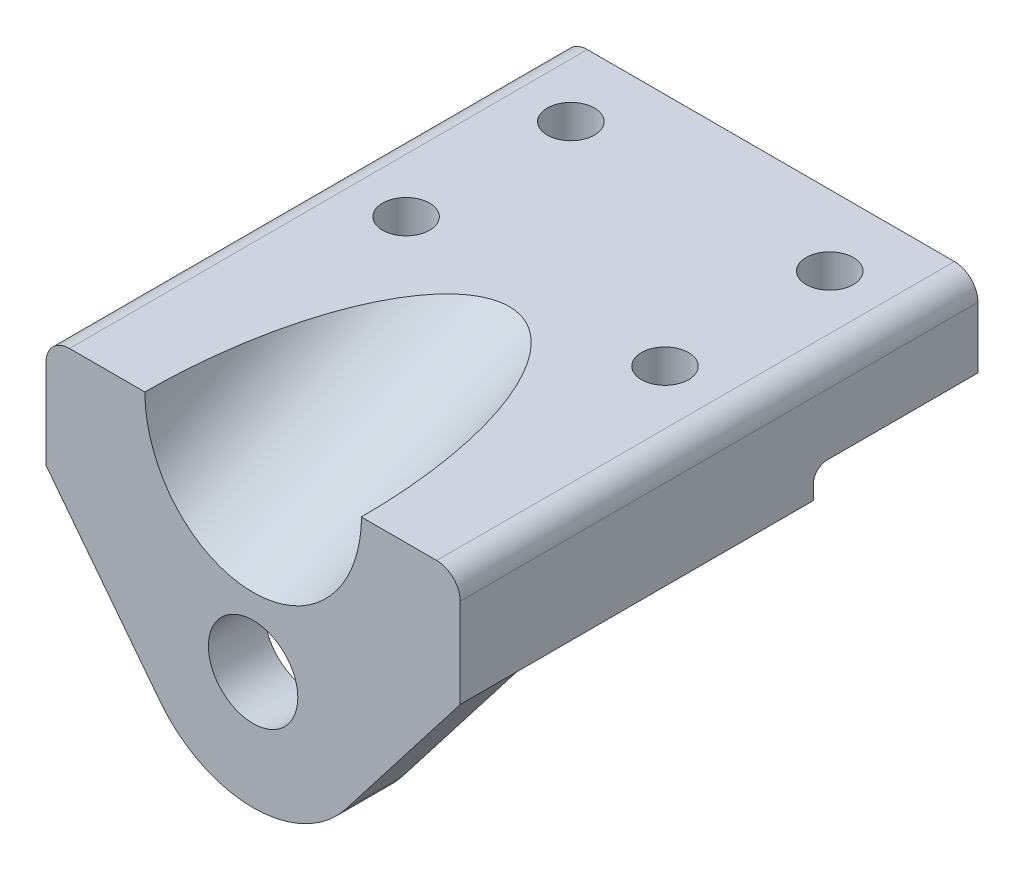
SolidWorks part; units mm, degrees
ref_plane "Front Plane" through (0, 0, 0) normal (0, 0, 1) x (1, 0, 0)
ref_plane "Top Plane" through (0, 0, 0) normal (0, 1, 0) x (1, 0, 0)
ref_plane "Right Plane" through (0, 0, 0) normal (1, 0, 0) x (0, 0, -1)
sketch "Sketch1" plane through (0, 0, 0) normal (0, 1, 0) x (1, 0, 0)
  line L0 (-44, 0) -> (44, 0)
  line L1 (44, 0) -> (44, 110)
  line L2 (44, 110) -> (-44, 110)
  line L3 (-44, 110) -> (-44, 0)
  circle A0 centre (-27.5, 95) radius 5
  circle A1 centre (-27.5, 60) radius 5
  circle A2 centre (27.5, 60) radius 5
  circle A3 centre (27.5, 95) radius 5
  point P4 (0, 0)
  point P15 (0, 0)
  point P16 (0, 0)
  dimension "D3" = 10
  dimension "D4" = 10
  dimension "D5" = 10
  dimension "D6" = 10
  dimension "D1" = 110
  dimension "D2" = 88
  dimension "D7" = 55
  dimension "D8" = 15
  dimension "D9" = 15
  dimension "D10" = 16.5
  dimension "D11" = 35
  dimension "D12" = 35
extrude "Boss-Extrude1" add sketch "Sketch1" against normal blind 24
sketch "Sketch3" plane through (0, 0, 0) normal (0, 0, 1) x (1, 0, 0)
  line L0 (-44, -24) -> (-19.7692, -55.3029)
  line L1 (44, -24) -> (19.7692, -55.3029)
  line L2 (-44, -24) -> (44, -24)
  arc A0 (-19.7692, -55.3029) -> (19.7692, -55.3029) centre (0, -40) ccw
  circle A1 centre (0, -40) radius 9.5
  dimension "D2" = 50
  dimension "D3" = 19
  dimension "D1" = 40
extrude "Boss-Extrude2" add sketch "Sketch3" against normal blind 12
fillet "Fillet1" radius 5 2 edges at (-44, 0, -55) (44, 0, -55)
sketch "Sketch4" plane through (0, 0, -110) normal (0, 0, -1) x (-1, 0, 0)
  line L0 (44, -24) -> (44, -5) construction
  line L1 (-44, -24) -> (44, -24)
  line L2 (-44, -24) -> (-44, -18)
  line L3 (-44, -18) -> (44, -18)
  line L4 (44, -24) -> (44, -18)
  dimension "D1" = 6
extrude "Cut-Extrude1" cut sketch "Sketch4" against normal blind 35
fillet "Fillet2" radius 3 1 edges at (0, -18, -75)
ref_plane "Plane1" through (0, 0, 0) normal (0, 0.4226, -0.9063) x (1, 0, 0)
sketch "Sketch5" plane through (0, 0, 0) normal (0, 0.4226, -0.9063) x (1, 0, 0)
  circle A0 centre (0, 0) radius 23
  dimension "D1" = 46
extrude "Cut-Extrude2" cut sketch "Sketch5" against normal blind 35 and the other way blind 109
